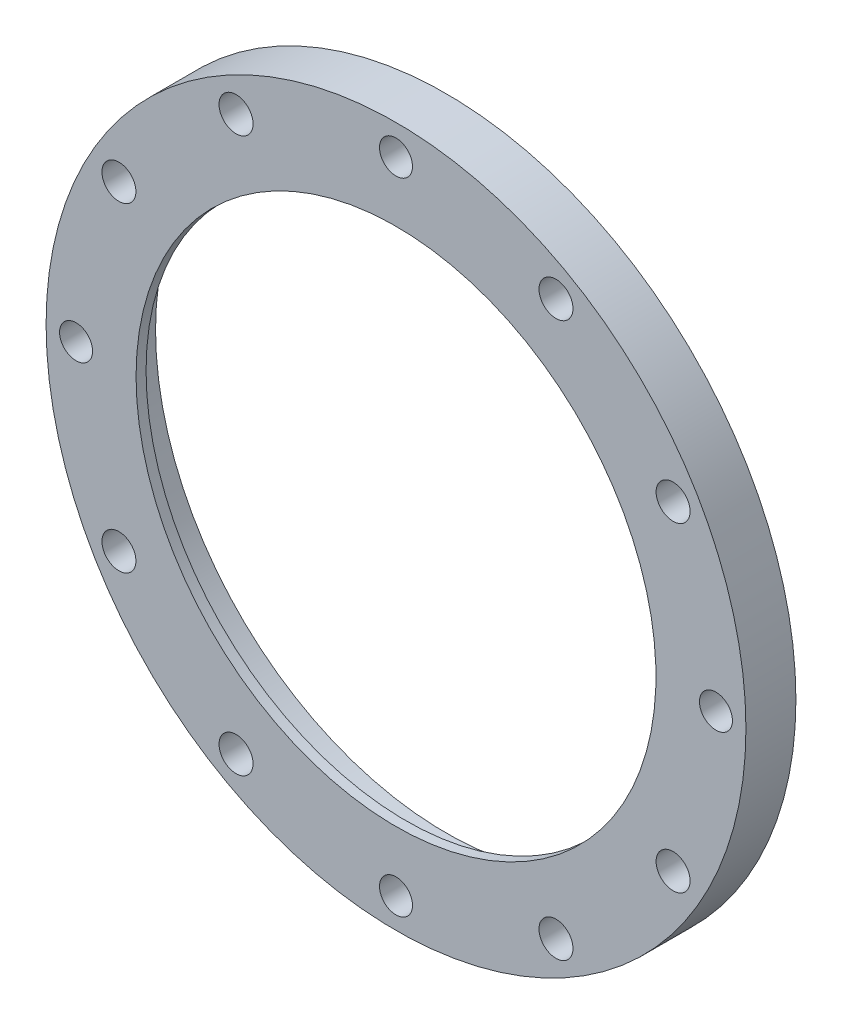
SolidWorks part; units mm, degrees
ref_plane "前视基准面" through (0, 0, 0) normal (0, 0, 1) x (1, 0, 0)
ref_plane "上视基准面" through (0, 0, 0) normal (0, 1, 0) x (1, 0, 0)
ref_plane "右视基准面" through (0, 0, 0) normal (1, 0, 0) x (0, 0, -1)
sketch "草图1" plane through (0, 0, 0) normal (0, 1, 0) x (1, 0, 0)
  line L0 (35, 5) -> (0, 5)
  line L1 (0, 5) -> (0, 0)
  line L2 (0, 0) -> (35, 0)
  line L3 (35, 0) -> (35, 5)
  line L4 (0, 5) -> (0, 0) construction
revolve "旋转1" add sketch "草图1" angle 360 about L4
hole_wizard "孔1" positions "草图3" profile "草图2" legacy
sketch "草图3" plane through (0, 0, -5) normal (0, 0, -1) x (-1, 0, 0)
  point P0 (16, -27.7128)
  point P1 (-16, -27.7128)
  point P2 (-27.7128, -16)
  point P3 (-27.7128, 16)
  point P4 (-16, 27.7128)
  point P5 (16, 27.7128)
  point P6 (27.7128, 16)
  point P7 (27.7128, -16)
sketch "草图2" plane through (-16, -27.7128, -5) normal (1, 0, 0) x (0, 1, 0)
  line L0 (0, 0) -> (0, 5)
  line L1 (0, 5) -> (1.7, 5)
  line L2 (1.7, 5) -> (1.7, 0)
  line L3 (1.7, 0) -> (0, 0)
  line L4 (0, 110) -> (0, -10) construction
  dimension "直径" = 3.4
  dimension "深度" = 5
hole_wizard "孔2" positions "草图5" profile "草图4" legacy
sketch "草图5" plane through (0, 0, -5) normal (0, 0, -1) x (-1, 0, 0)
  point P0 (0, 0)
sketch "草图4" plane through (0, 0, -5) normal (1, 0, 0) x (0, 1, 0)
  line L0 (0, 0) -> (0, 5)
  line L1 (0, 5) -> (26, 5)
  line L2 (26, 5) -> (26, 4)
  line L3 (26, 4) -> (29.05, 4)
  line L4 (29.05, 4) -> (29.05, 0)
  line L5 (29.05, 0) -> (0, 0)
  line L6 (0, 110) -> (0, -10) construction
  dimension "直径" = 52
  dimension "深度" = 5
  dimension "柱坑直径" = 58.1
  dimension "柱坑深度" = 4
sketch "草图9" plane through (0, 0, -5) normal (0, 0, -1) x (-1, 0, 0)
  line L0 (0, 0) -> (32, 0) construction
  circle A0 centre (32, 0) radius 1.65
  circle A1 centre (0, -32) radius 1.65
  circle A2 centre (-32, 0) radius 1.65
  circle A3 centre (0, 32) radius 1.65
  point P13 (0, 0)
  dimension "D1" = 4
extrude "切除-拉伸1" cut sketch "草图9" against normal blind 10
